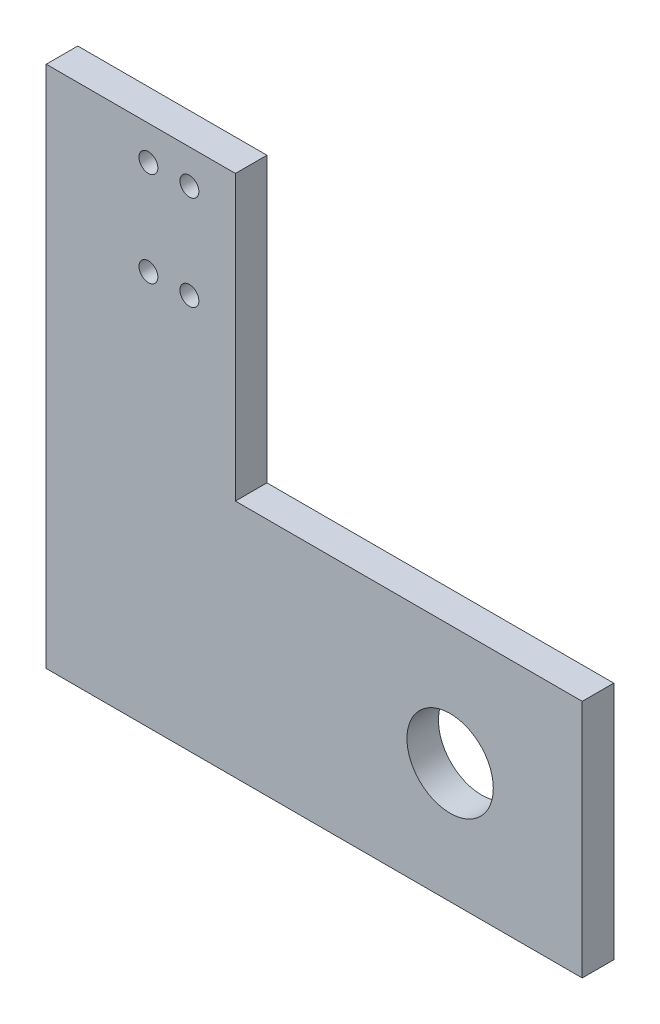
SolidWorks part; units mm, degrees
ref_plane "前视基准面" through (0, 0, 0) normal (0, 0, 1) x (1, 0, 0)
ref_plane "上视基准面" through (0, 0, 0) normal (0, 1, 0) x (1, 0, 0)
ref_plane "右视基准面" through (0, 0, 0) normal (1, 0, 0) x (0, 0, -1)
sketch "草图7" plane through (0, 0, 0) normal (0, 0, 1) x (1, 0, 0)
  line L1 (2345.4712, 4698.9762) -> (2345.4712, 4743.9762)
  line L2 (2315.4712, 4660.9762) -> (2400.4712, 4660.9762)
  line L3 (2345.4712, 4698.9762) -> (2400.4712, 4698.9762)
  line L4 (2400.4712, 4698.9762) -> (2400.4712, 4660.9762)
  line L5 (2345.4712, 4743.9762) -> (2315.4712, 4743.9762)
  line L6 (2315.4712, 4660.9762) -> (2315.4712, 4743.9762)
  circle A1 centre (2338.1724, 4738.5762) radius 1.5
  circle A2 centre (2338.1724, 4723.5762) radius 1.5
  circle A3 centre (2331.6724, 4738.5762) radius 1.5
  circle A4 centre (2331.6724, 4723.5762) radius 1.5
  circle A5 centre (2379.5182, 4679.9762) radius 6.85
extrude "凸台-拉伸6" add sketch "草图7" along normal blind 5
